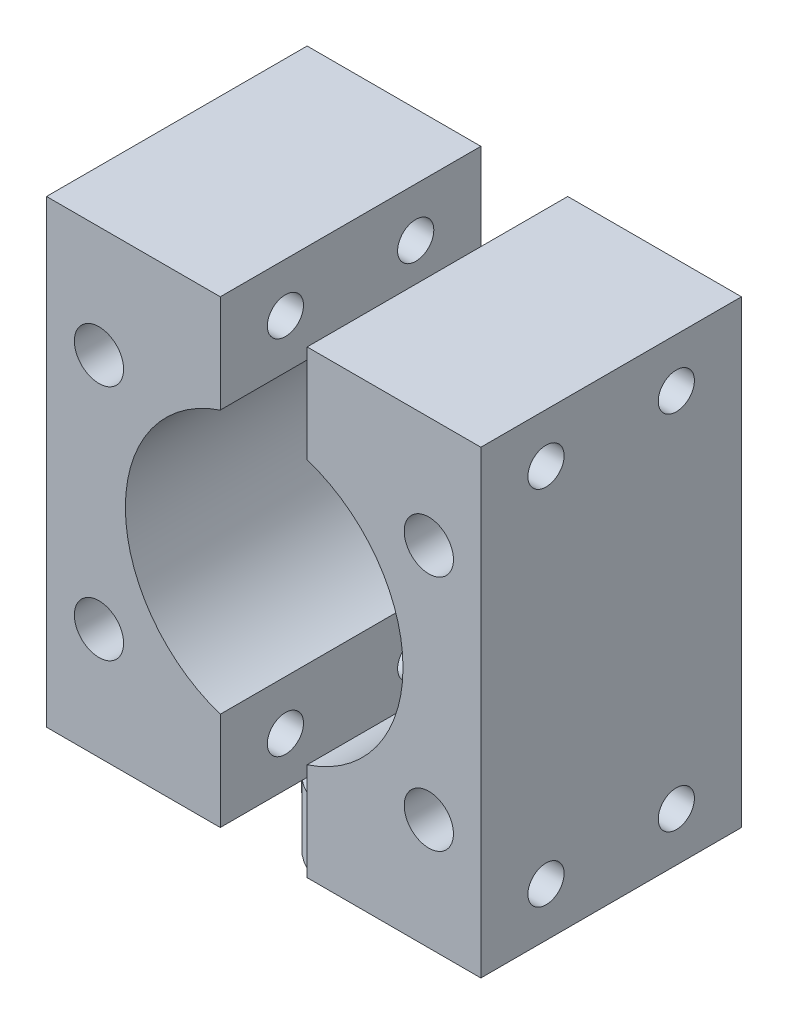
SolidWorks part; units mm, degrees
ref_plane "Front Plane" through (0, 0, 0) normal (0, 0, 1) x (1, 0, 0)
ref_plane "Top Plane" through (0, 0, 0) normal (0, 1, 0) x (1, 0, 0)
ref_plane "Right Plane" through (0, 0, 0) normal (1, 0, 0) x (0, 0, -1)
sketch "Sketch1" plane through (0, 0, 0) normal (0, 1, 0) x (1, 0, 0)
  line L0 (0, 4.75) -> (0, -4.75) construction
  line L1 (1.5, 4.5069) -> (1.5, -4.5069)
  line L2 (-1.5, 4.5069) -> (-1.5, -4.5069)
  circle A0 centre (0, 0) radius 4.75
  dimension "D1" = 9.5
  dimension "D2" = 1.5
ref_plane "GroundPlane" through (0, 4.5, 0) normal (0, 1, 0) x (-1, 0, 0)
sketch "Sketch2" plane through (0, 4.5, 0) normal (0, 1, 0) x (-1, 0, 0)
  line L0 (0, 7.5) -> (6.4952, -3.75) construction
  line L1 (0, 7.5) -> (0, -7.5) construction
  line L2 (0, 12.7) -> (0, -12.7) construction
  line L3 (0, 7.5) -> (-6.4952, -3.75) construction
  line L4 (-9.2393, -11.2686) -> (9.8107, -11.2686) construction
  line L5 (-9.2393, -11.2686) -> (-9.2393, -30.3186) construction
  line L6 (-9.2393, -30.3186) -> (9.8107, -30.3186) construction
  line L7 (9.8107, -11.2686) -> (9.8107, -30.3186) construction
  line L8 (-6.4952, -3.75) -> (6.4952, -3.75) construction
  line L9 (0, -7.5) -> (6.4952, 3.75) construction
  line L10 (6.4952, 3.75) -> (-6.4952, 3.75) construction
  line L11 (-6.4952, 3.75) -> (0, -7.5) construction
  line L12 (3, -8.6561) -> (3, 9.3439)
  line L13 (3, -8.6561) -> (15, -8.6561)
  line L14 (3, 9.3439) -> (15, 9.3439)
  line L15 (15, 9.3439) -> (15, -8.6561)
  line L16 (-3, -8.6561) -> (-3, 9.3439)
  line L17 (-3, -8.6561) -> (-15, -8.6561)
  line L18 (-3, 9.3439) -> (-15, 9.3439)
  line L19 (-15, 9.3439) -> (-15, -8.6561)
  circle A0 centre (0, 0) radius 7.5 construction
  dimension "D1" = 15
  dimension "D2" = 30
  dimension "D3" = 25.4
  dimension "D4" = 19.05
  dimension "D5" = 19.05
  dimension "D6" = 30
  dimension "D7" = 30
  dimension "D8" = 3
  dimension "D9" = 18
  dimension "D10" = 12
ref_plane "TopPlane" through (0, 36.25, 0) normal (0, 1, 0) x (-1, 0, 0)
extrude "Extrude1" add sketch "Sketch2" along normal blind 31.75
extrude "Extrude2" add sketch "Sketch1" along normal blind 4.5 contours L1 A0 | L2 A0
sketch "Sketch4" plane through (0, 0, 9.3439) normal (0, 0, 1) x (1, 0, 0)
  line L0 (-14.9586, 36.25) -> (15.0262, 4.5) construction
  line L1 (9.9, 36.25) -> (-9.9, 36.25) construction
  line L2 (9.9, 4.5) -> (-9.9, 4.5) construction
  line L3 (15.0262, 36.25) -> (-14.9586, 4.5) construction
  circle A0 centre (0.0338, 20.375) radius 9.5885
  point P8 (0.0338, 20.375)
  dimension "D1" = 19.177
extrude "Extrude3" cut sketch "Sketch4" against normal blind 17
sketch "Sketch6" plane through (15, 0, 0) normal (1, 0, 0) x (0, 0, -1)
  line L0 (-9.3439, 36.25) -> (-9.3439, 4.5) construction
  line L1 (-9.3439, 20.375) -> (8.6561, 20.375) construction
  line L2 (8.6561, 36.25) -> (8.6561, 4.5) construction
  line L3 (-0.3439, 36.25) -> (-0.3439, 4.5) construction
  line L4 (-9.3439, 36.25) -> (8.6561, 36.25) construction
  line L5 (-9.3439, 4.5) -> (8.6561, 4.5) construction
  line L6 (-0.3439, 36.25) -> (-9.3439, 29.4932) construction
  point P12 (-4.8439, 32.8716)
  point P15 (4.1561, 32.8716)
  point P16 (4.1561, 7.8784)
  point P17 (-4.8439, 7.8784)
hole_wizard "M3x0.5 Tapped Hole1" positions "3DSketch1" profile "Sketch8" tap size "M3x0.5" standard "Ansi Metric" end condition through all
sketch3d "3DSketch1"
  point P0 (15, 32.8716, 4.8439)
  point P3 (15, 32.8716, -4.1561)
  point P6 (15, 7.8784, 4.8439)
  point P9 (15, 7.8784, -4.1561)
sketch "Sketch8" plane through (15, 32.8716, 4.8439) normal (0, 1, 0) x (0, 0, -1)
  line L0 (0, 0) -> (0, 30)
  line L1 (0, 30) -> (1.25, 30)
  line L2 (1.25, 30) -> (1.25, 0)
  line L5 (1.25, 0) -> (0, 0)
  line L11 (0, -6.35) -> (0, 107.95) construction
  dimension "Thru Tap Drill Dia." = 2.5
  dimension "Thru Tap Drill Depth" = 30
cosmetic thread "Hole Thread1" parameters "D2"=3
cosmetic thread "Hole Thread2" parameters "D2"=3
cosmetic thread "Hole Thread3" parameters "D2"=3
cosmetic thread "Hole Thread4" parameters "D2"=3
sketch "Sketch9" plane through (0, 0, 9.3439) normal (0, 0, 1) x (1, 0, 0)
  line L0 (-15, 31.1716) -> (-7.7544, 25.9681) construction
  line L1 (-15, 9.5784) -> (-7.7544, 14.7819) construction
  line L2 (15, 9.5784) -> (7.81, 14.7652) construction
  line L3 (15, 36.25) -> (15, 4.5) construction
  line L4 (15, 31.1716) -> (7.81, 25.9848) construction
  line L5 (15, 36.25) -> (15, 29.4932) construction
  arc A0 (-3, 29.4709) -> (-3, 11.2791) centre (0.0338, 20.375) ccw construction
  arc A1 (3, 11.2568) -> (3, 29.4932) centre (0.0338, 20.375) ccw construction
  point P20 (-11.3772, 28.5699)
  point P21 (-11.3772, 12.1801)
  point P22 (11.405, 12.1718)
  point P23 (11.405, 28.5782)
hole_wizard "M3 Clearance Hole1" positions "3DSketch2" profile "Sketch11" hole size "M3" standard "Ansi Metric" end condition through all
sketch3d "3DSketch2"
  point P0 (-11.3772, 28.5699, 9.3439)
  point P3 (-11.3772, 12.1801, 9.3439)
  point P6 (11.405, 12.1718, 9.3439)
  point P9 (11.405, 28.5782, 9.3439)
sketch "Sketch11" plane through (-11.3772, 28.5699, 9.3439) normal (1, 0, 0) x (0, -1, 0)
  line L0 (0, 0) -> (0, 18)
  line L1 (0, 18) -> (1.7, 18)
  line L2 (1.7, 18) -> (1.7, 0)
  line L5 (1.7, 0) -> (0, 0)
  line L11 (0, -6.35) -> (0, 107.95) construction
  dimension "Thru Hole Dia." = 3.4
  dimension "Thru Hole Depth" = 18
sketch "Sketch14" plane through (0, 4.5, 0) normal (0, 1, 0) x (-1, 0, 0)
  point P0 (6.4952, 3.75)
  point P1 (-6.4952, 3.75)
  point P3 (0, -7.5)
